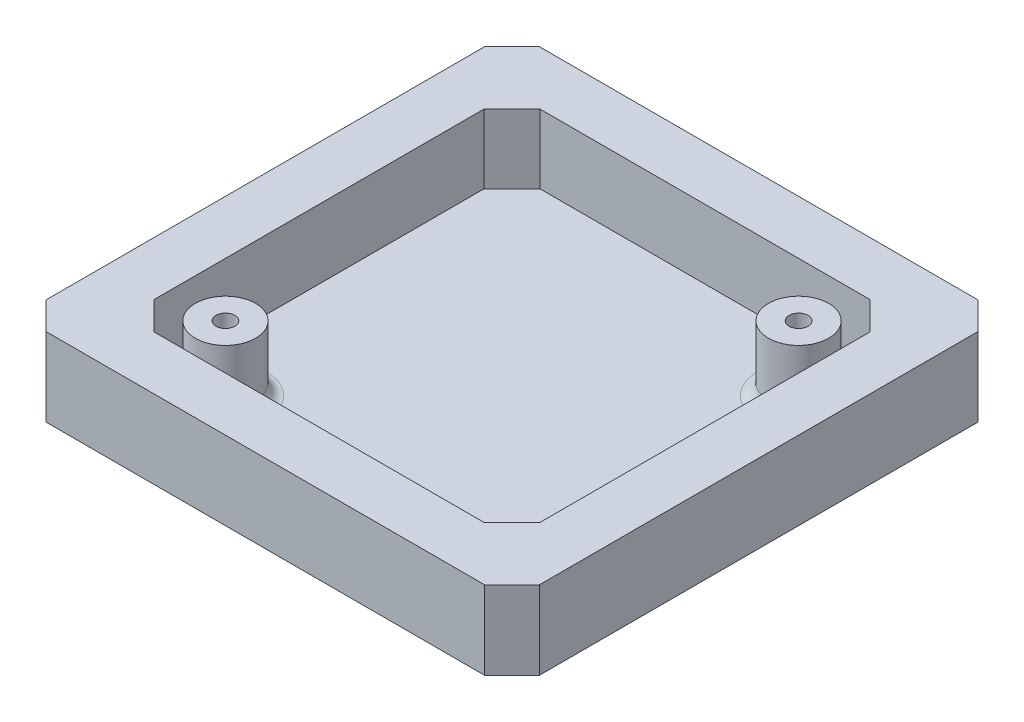
SolidWorks part; units mm, degrees
ref_plane "Front Plane" through (0, 0, 0) normal (0, 0, 1) x (1, 0, 0)
ref_plane "Top Plane" through (0, 0, 0) normal (0, 1, 0) x (1, 0, 0)
ref_plane "Right Plane" through (0, 0, 0) normal (1, 0, 0) x (0, 0, -1)
sketch "Sketch1" plane through (0, 0, 0) normal (0, 1, 0) x (1, 0, 0)
  line L1 (0, 0) -> (90, 0)
  line L2 (0, 0) -> (0, 90)
  line L3 (0, 90) -> (90, 90)
  line L4 (90, 0) -> (90, 90)
  line L5 (0, 0) -> (90, 90) construction
  line L6 (0, 90) -> (90, 0) construction
  point P4 (45, 45)
  dimension "D1" = 90
extrude "Boss-Extrude1" add sketch "Sketch1" along normal blind 14.3
sketch "Sketch2" plane through (0, 14.3, 0) normal (0, 1, 0) x (1, 0, 0)
  line L0 (0, 0) -> (90, 90) construction
  line L1 (10, 10) -> (80, 10)
  line L2 (10, 10) -> (10, 80)
  line L3 (10, 80) -> (80, 80)
  line L4 (80, 10) -> (80, 80)
  line L5 (10, 10) -> (80, 80) construction
  line L6 (10, 80) -> (80, 10) construction
  point P4 (45, 45)
  point P9 (45, 45)
  dimension "D1" = 70
extrude "Cut-Extrude1" cut sketch "Sketch2" against normal blind 12.6
sketch "Sketch3" plane through (0, 1.7, 0) normal (0, 1, 0) x (1, 0, 0)
  line L0 (10, 10) -> (80, 80) construction
  circle A0 centre (18.864, 18.864) radius 1.725
  circle A1 centre (71.136, 71.136) radius 1.725
  point P8 (45, 45)
  dimension "D1" = 3.45
  dimension "D2" = 12.5355
  dimension "D3" = 12.5355
extrude "Cut-Extrude2" cut sketch "Sketch3" against normal through all
chamfer "Chamfer1" distance 5 angle 45 4 edges at (0, 7.15, 0) (0, 7.15, -90) (90, 7.15, -90) (90, 7.15, 0)
sketch "Sketch4" plane through (0, 1.7, 0) normal (0, 1, 0) x (1, 0, 0)
  line L0 (10, 80) -> (80, 10) construction
  circle A0 centre (71.136, 71.136) radius 5.5
  circle A1 centre (71.136, 71.136) radius 1.725
  circle A2 centre (71.136, 71.136) radius 1.725 construction
  circle A3 centre (18.864, 18.864) radius 1.725
  circle A4 centre (18.864, 18.864) radius 5.5
  dimension "D1" = 11
extrude "Boss-Extrude2" add sketch "Sketch4" along normal offset from surface (11.8 mm away) 0.8 up to face at (45, 14.3, -45)
fillet "Fillet1" radius 2 2 edges at (18.864, 1.7, -24.364) (71.136, 1.7, -76.636)
sketch "Sketch5" plane through (0, 0, 0) normal (0, -1, 0) x (1, 0, 0)
  circle A0 centre (18.864, -18.864) radius 3.25
  circle A1 centre (71.136, -71.136) radius 3.25
  dimension "D1" = 6.5
extrude "Cut-Extrude3" cut sketch "Sketch5" against normal blind 4
chamfer "Chamfer2" distance 5 angle 45 4 edges at (80, 8, -80) (80, 8, -10) (10, 8, -80) (10, 8, -10)
sketch "Sketch6" plane through (0, 1.7, 0) normal (0, 1, 0) x (1, 0, 0)
  line L24 (15, 10) -> (10, 15)
  line L25 (10, 15) -> (10, 75)
  line L34 (10, 75) -> (15, 80)
  line L35 (15, 80) -> (75, 80)
  line L36 (75, 80) -> (80, 75)
  line L37 (80, 75) -> (80, 15)
  line L38 (80, 15) -> (75, 10)
  line L39 (75, 10) -> (15, 10)
  line L40 (80.2, 14.9172) -> (80.2, 75.0828)
  line L41 (80.2, 75.0828) -> (75.0828, 80.2)
  line L42 (75.0828, 80.2) -> (14.9172, 80.2)
  line L43 (14.9172, 80.2) -> (9.8, 75.0828)
  line L44 (9.8, 75.0828) -> (9.8, 14.9172)
  line L45 (9.8, 14.9172) -> (14.9172, 9.8)
  line L46 (14.9172, 9.8) -> (75.0828, 9.8)
  line L47 (75.0828, 9.8) -> (80.2, 14.9172)
  line L48 (80.2, 14.9172) -> (80.2, 75.0828)
  line L49 (80.2, 75.0828) -> (75.0828, 80.2)
  line L50 (75.0828, 80.2) -> (14.9172, 80.2)
  line L51 (14.9172, 80.2) -> (9.8, 75.0828)
  line L52 (9.8, 75.0828) -> (9.8, 14.9172)
  line L53 (9.8, 14.9172) -> (14.9172, 9.8)
  line L54 (14.9172, 9.8) -> (75.0828, 9.8)
  line L55 (75.0828, 9.8) -> (80.2, 14.9172)
  dimension "D1" = 0.2
extrude "Cut-Extrude4" cut sketch "Sketch6" along normal through all
